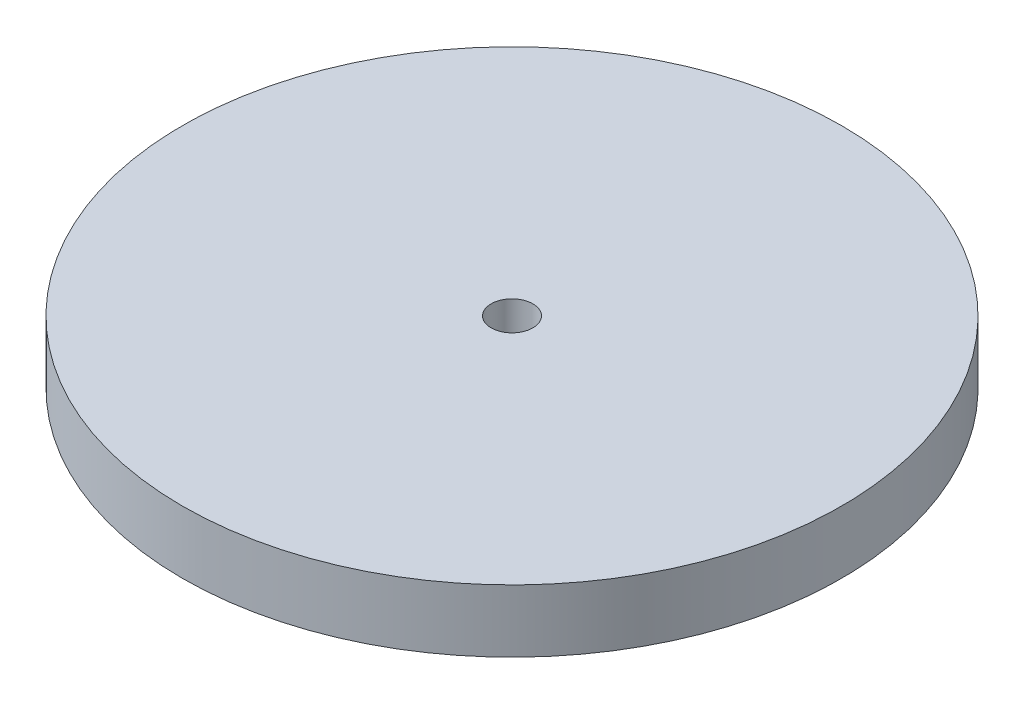
SolidWorks part; units mm, degrees
ref_plane "Front Plane" through (0, 0, 0) normal (0, 0, 1) x (1, 0, 0)
ref_plane "Top Plane" through (0, 0, 0) normal (0, 1, 0) x (1, 0, 0)
ref_plane "Right Plane" through (0, 0, 0) normal (1, 0, 0) x (0, 0, -1)
sketch "Sketch1" plane through (0, 0, 0) normal (0, 1, 0) x (1, 0, 0)
  circle A0 centre (0, 0) radius 157.89
  circle A1 centre (0, 0) radius 10
  dimension "D1" = 315.78
  dimension "D2" = 20
extrude "Boss-Extrude1" add sketch "Sketch1" along normal blind 30
